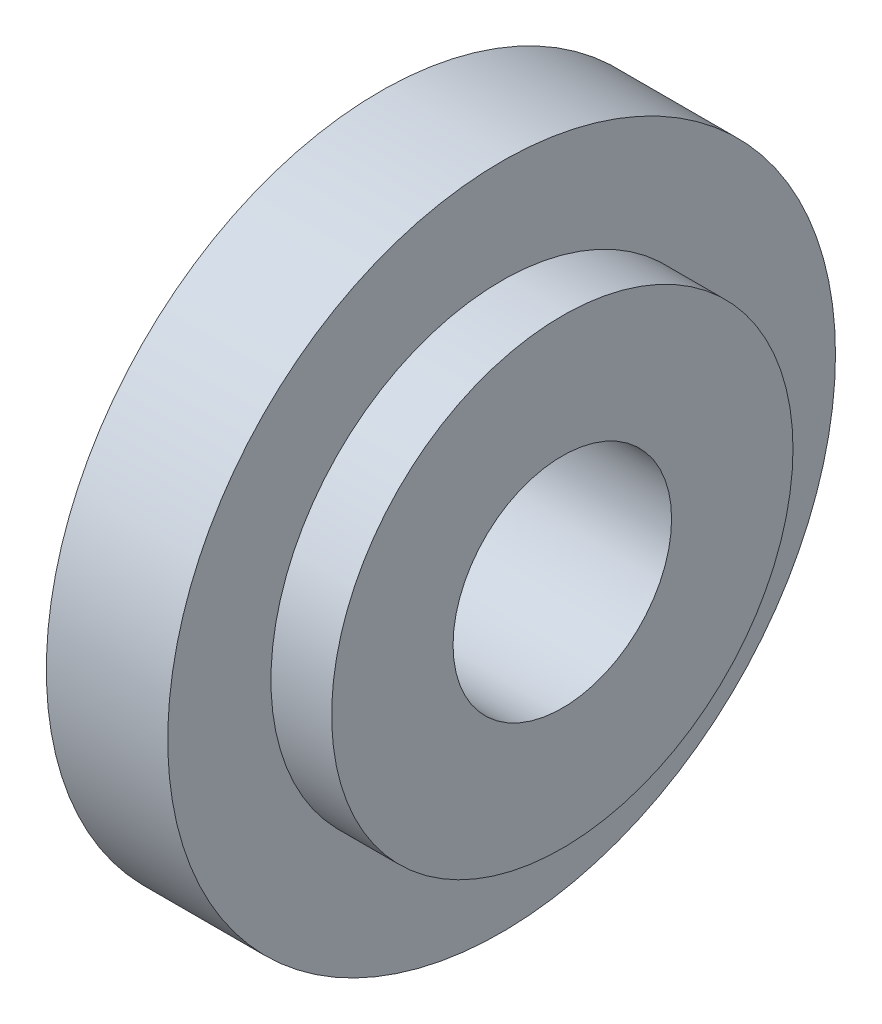
SolidWorks part; units mm, degrees
ref_plane "Front Plane" through (0, 0, 0) normal (0, 0, 1) x (1, 0, 0)
ref_plane "Top Plane" through (0, 0, 0) normal (0, 1, 0) x (1, 0, 0)
ref_plane "Right Plane" through (0, 0, 0) normal (1, 0, 0) x (0, 0, -1)
sketch "Sketch1" plane through (0, 0, 0) normal (1, 0, 0) x (0, 0, -1)
  circle A0 centre (0, 0) radius 5.5
extrude "Boss-Extrude1" add sketch "Sketch1" along normal blind 2
sketch "Sketch2" plane through (2, 0, 0) normal (1, 0, 0) x (0, 0, -1)
  circle A0 centre (0, 0) radius 3.8
extrude "Boss-Extrude2" add sketch "Sketch2" along normal blind 1
sketch "Sketch3" plane through (0, 0, 0) normal (-1, 0, 0) x (0, 0, 1)
  circle A0 centre (0, 0) radius 1.8
extrude "Cut-Extrude1" cut sketch "Sketch3" against normal blind 20
